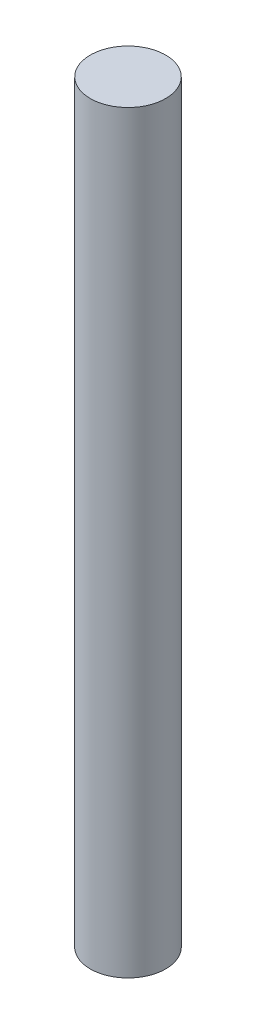
SolidWorks part; units mm, degrees
ref_plane "Front Plane" through (0, 0, 0) normal (0, 0, 1) x (1, 0, 0)
ref_plane "Top Plane" through (0, 0, 0) normal (0, 1, 0) x (1, 0, 0)
ref_plane "Right Plane" through (0, 0, 0) normal (1, 0, 0) x (0, 0, -1)
sketch "Sketch1" plane through (0, 0, 0) normal (0, 1, 0) x (1, 0, 0)
  circle A0 centre (0, 0) radius 20
  point P3 (0, 0)
  dimension "D1" = 40
extrude "Boss-Extrude1" add sketch "Sketch1" along normal blind 400 contours A0
